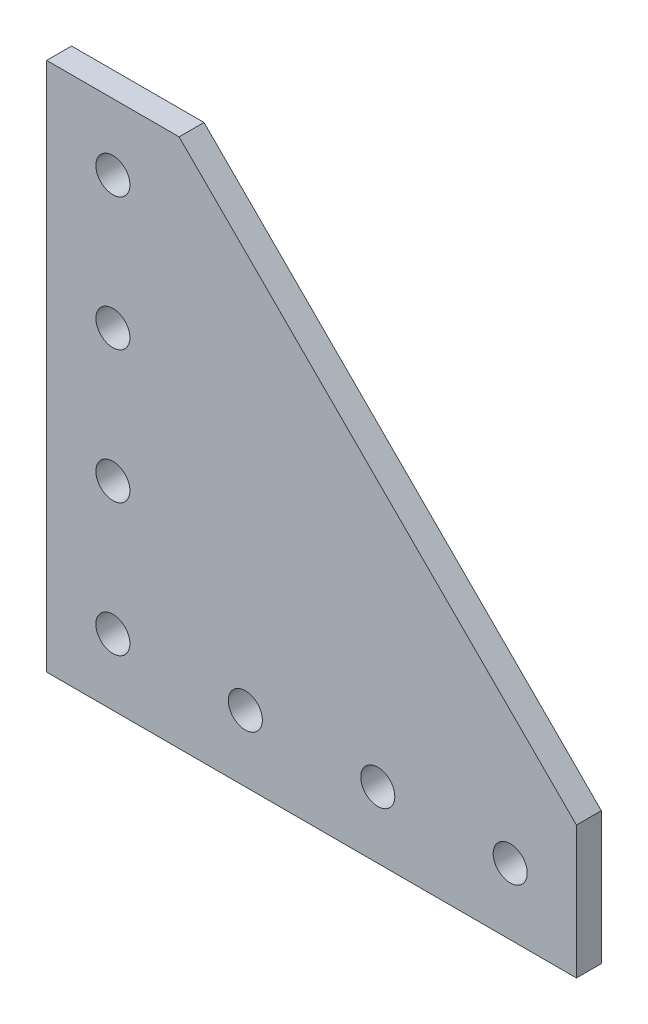
SolidWorks part; units mm, degrees
material "6061-T6 (SS)"
ref_plane "Front Plane" through (0, 0, 0) normal (0, 0, 1) x (1, 0, 0)
ref_plane "Top Plane" through (0, 0, 0) normal (0, 1, 0) x (1, 0, 0)
ref_plane "Right Plane" through (0, 0, 0) normal (1, 0, 0) x (0, 0, -1)
sketch "Sketch1" plane through (0, 0, 0) normal (0, 0, 1) x (1, 0, 0)
  line L0 (-50.8, -50.8) -> (50.8, -50.8) construction
  line L1 (-50.8, 50.8) -> (-50.8, -50.8) construction
  line L2 (50.8, -50.8) -> (50.8, -25.4) construction
  line L3 (-38.1, -34.8361) -> (-38.1, -41.3639) construction
  point P3 (0, -50.8)
  point P8 (-50.8, 0)
  point P9 (-38.1, -38.1)
  point P10 (50.8, -38.1)
  point P11 (0, 50.8)
  point P12 (-12.7, -38.1)
sketch "Sketch2" plane through (0, 0, 0) normal (1, 0, 0) x (0, 0, -1)
  line L0 (2.3876, 0) -> (-2.3876, 0) construction
  point P4 (0, 0)
  dimension "Thickness" = 4.7752
sketch "Sketch3" plane through (0, 0, 0) normal (0, 0, 1) x (1, 0, 0)
  line L0 (50.8, -25.4) -> (50.8, -50.8)
  line L1 (50.8, -50.8) -> (-50.8, -50.8)
  line L2 (-50.8, -50.8) -> (-50.8, 50.8)
  line L3 (-50.8, 50.8) -> (-25.4, 50.8)
  line L4 (-25.4, 50.8) -> (50.8, -25.4)
extrude "Boss-Extrude1" add sketch "Sketch3" against normal up to vertex (2.3876 mm away) and the other way up to vertex (2.3876 mm away) up to point (0, 0, -2.3876) other way up to point (0, 0, 2.3876)
sketch "Sketch4" plane through (0, 0, 2.3876) normal (0, 0, 1) x (1, 0, 0)
  line L0 (-38.1, -34.8361) -> (-38.1, -41.3639) construction
  line L1 (-50.8, -50.8) -> (0, 0) construction
  line L2 (-38.1, -38.1) -> (-12.7, -38.1) construction
  line L3 (-38.1, -38.1) -> (-38.1, -12.7) construction
  circle A0 centre (-38.1, -38.1) radius 3.2639
  circle A5 centre (-12.7, -38.1) radius 3.2639
  circle A6 centre (12.7, -38.1) radius 3.2639
  circle A7 centre (-38.1, -12.7) radius 3.2639
  circle A8 centre (-38.1, 12.7) radius 3.2639
  circle A9 centre (38.1, -38.1) radius 3.2639
  circle A10 centre (-38.1, 38.1) radius 3.2639
  dimension "D2" = 25.4
  dimension "D4" = 25.4
  dimension "D1" = 4
  dimension "D3" = 4
extrude "Cut-Extrude1" cut sketch "Sketch4" against normal through all
equation "\"D2@Sketch4\"=\"Hole Spacing@Sketch1\""
equation "\"D1@Sketch4\"=\"#Holes@Sketch1\""
equation "\"D4@Sketch4\"=\"Hole Spacing@Sketch1\""
equation "\"D3@Sketch4\"=\"#Holes@Sketch1\""
